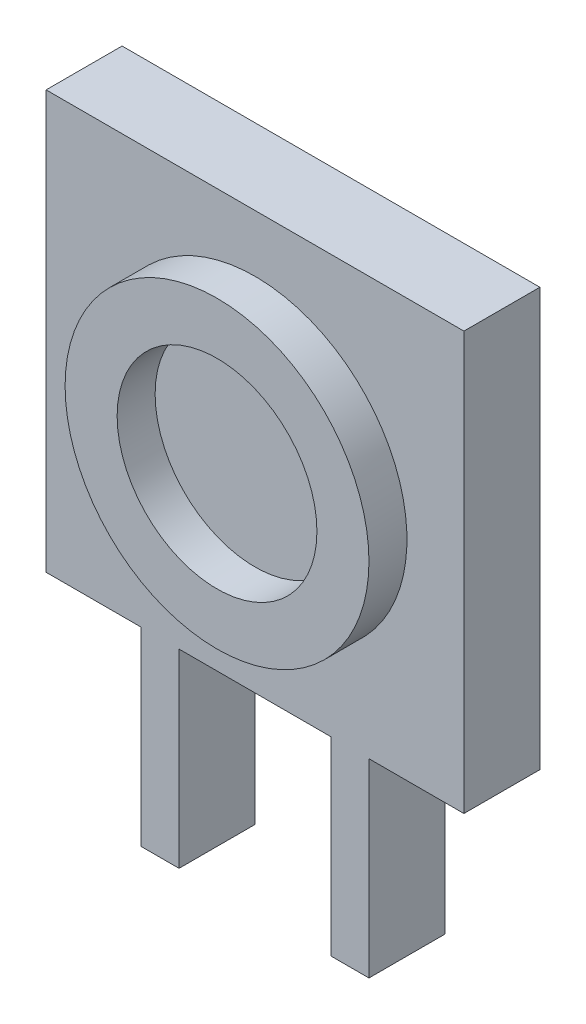
SolidWorks part; units mm, degrees
ref_plane "Front Plane" through (0, 0, 0) normal (0, 0, 1) x (1, 0, 0)
ref_plane "Top Plane" through (0, 0, 0) normal (0, 1, 0) x (1, 0, 0)
ref_plane "Right Plane" through (0, 0, 0) normal (1, 0, 0) x (0, 0, -1)
sketch "Sketch1" plane through (0, 0, 0) normal (0, 0, 1) x (1, 0, 0)
  line L0 (-2, -5.5) -> (2, -5.5)
  line L1 (-5.5, -5.5) -> (-3, -5.5)
  line L2 (-5.5, -5.5) -> (-5.5, 5.5)
  line L3 (-5.5, 5.5) -> (5.5, 5.5)
  line L4 (5.5, -5.5) -> (5.5, 5.5)
  line L5 (3, -5.5) -> (5.5, -5.5)
  line L6 (-3, -5.5) -> (-3, -10.5)
  line L7 (-3, -10.5) -> (-2, -10.5)
  line L8 (-2, -5.5) -> (-2, -10.5)
  line L9 (0, 2.2775) -> (0, -2.5413) construction
  line L10 (2, -5.5) -> (2, -10.5)
  line L11 (2, -10.5) -> (3, -10.5)
  line L12 (3, -5.5) -> (3, -10.5)
  line L13 (-5.5, -5.5) -> (5.5, 5.5) construction
  point P12 (0, -5.5)
  point P15 (0, 5.5)
  point P16 (0, 0)
  dimension "D1" = 11
  dimension "D2" = 11
  dimension "D3" = 1
  dimension "D4" = 1
  dimension "D5" = 5
  dimension "D6" = 4
extrude "Extrude1" add sketch "Sketch1" along normal blind 2
sketch "Sketch2" plane through (0, 0, 2) normal (0, 0, 1) x (1, 0, 0)
  circle A0 centre (0, 0) radius 4
  circle A1 centre (0, 0) radius 2.63
  dimension "D1" = 8
  dimension "D2" = 5.26
extrude "Extrude2" add sketch "Sketch2" along normal blind 1
